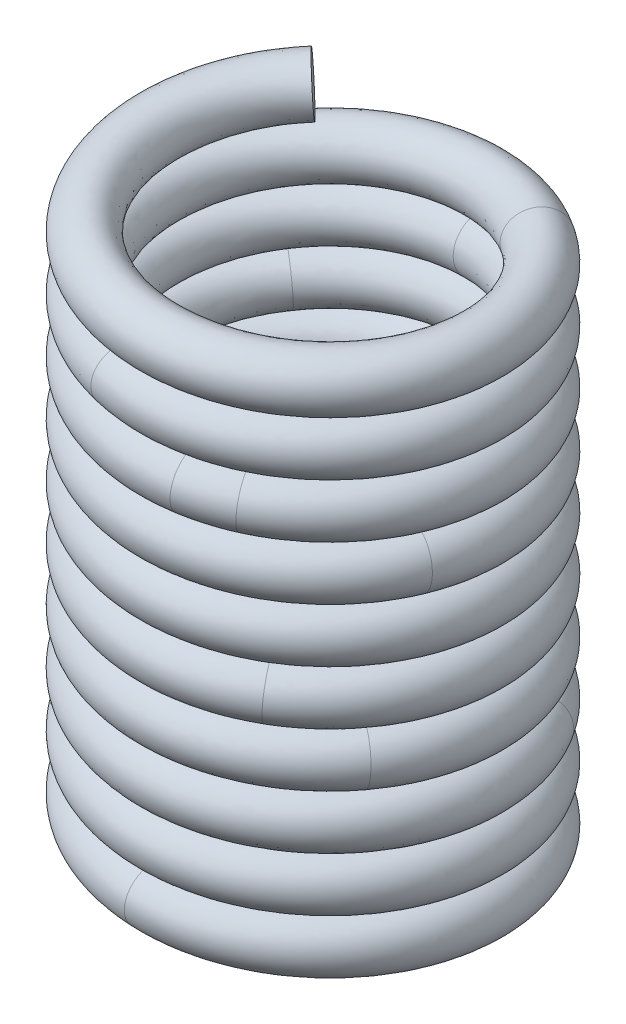
SolidWorks part; units mm, degrees
ref_plane "정면" through (0, 0, 0) normal (0, 0, 1) x (1, 0, 0)
ref_plane "윗면" through (0, 0, 0) normal (0, 1, 0) x (1, 0, 0)
ref_plane "우측면" through (0, 0, 0) normal (1, 0, 0) x (0, 0, -1)
sketch "스케치1" plane through (0, 0, 0) normal (0, 1, 0) x (1, 0, 0)
  circle A0 centre (0, 0) radius 60
  dimension "D1" = 120
curve "나선형 곡선1" pitch 20 height 200 turns 10
ref_plane "평면2" through (-42.4264, 0, -42.4264) normal (0.7061, 0.053, -0.7061) x (-0.7081, 0.0528, -0.7041)
sketch "스케치3" plane through (-42.4264, 0, -42.4264) normal (0.7061, 0.053, -0.7061) x (-0.7081, 0.0528, -0.7041)
  circle A0 centre (0, 0) radius 10
  point P2 (0, 0)
  point P3 (0, 0)
  dimension "D1" = 20
sweep "스윕1" add profiles "스케치3" path "나선형 곡선1"
